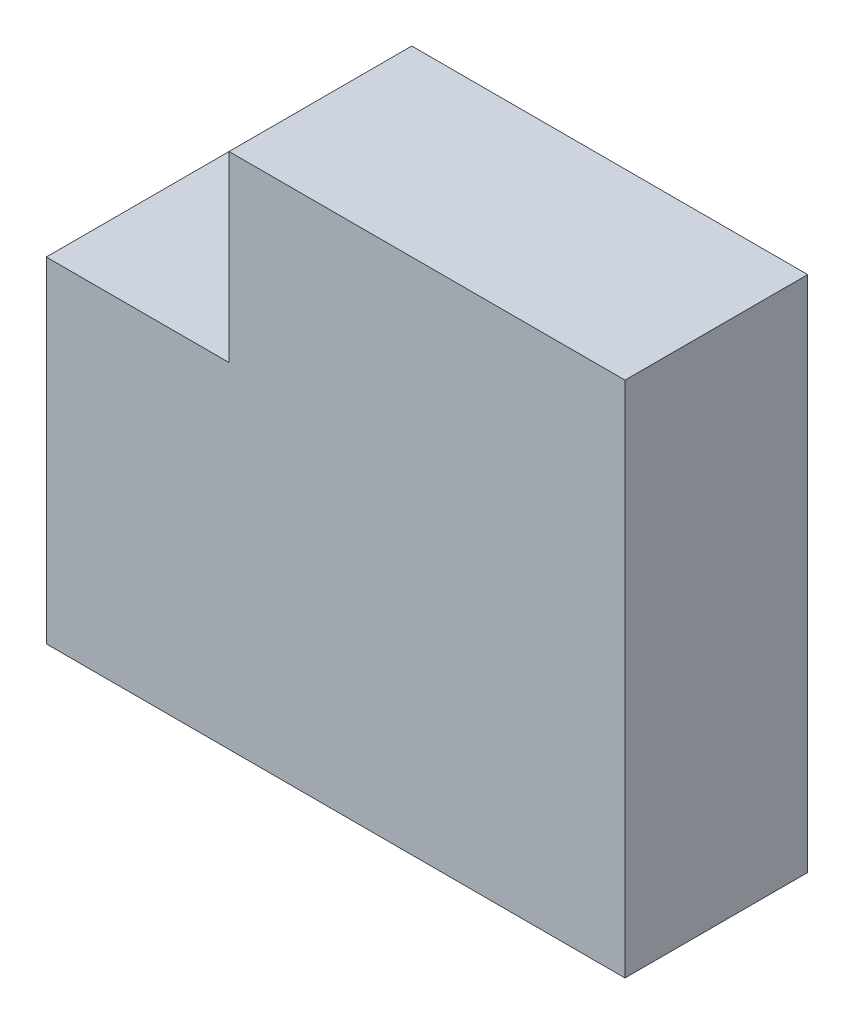
SolidWorks part; units mm, degrees
ref_plane "Plano frontal" through (0, 0, 0) normal (0, 0, 1) x (1, 0, 0)
ref_plane "Plano superior" through (0, 0, 0) normal (0, 1, 0) x (1, 0, 0)
ref_plane "Plano direito" through (0, 0, 0) normal (1, 0, 0) x (0, 0, -1)
sketch "Esboço1" plane through (0, 0, 0) normal (0, 0, 1) x (1, 0, 0)
  line L1 (0, 0) -> (19, 0)
  line L2 (0, 0) -> (0, 17)
  line L3 (0, 17) -> (19, 17)
  line L5 (0, 17) -> (6, 17)
  line L6 (0, 17) -> (0, 11)
  line L7 (0, 11) -> (6, 11)
  line L8 (6, 17) -> (6, 11)
  line L12 (19, 17) -> (19, 0)
  dimension "D1" = 17
  dimension "D2" = 19
  dimension "D3" = 6
extrude "Ressalto-extrusão1" add sketch "Esboço1" along normal blind 6
